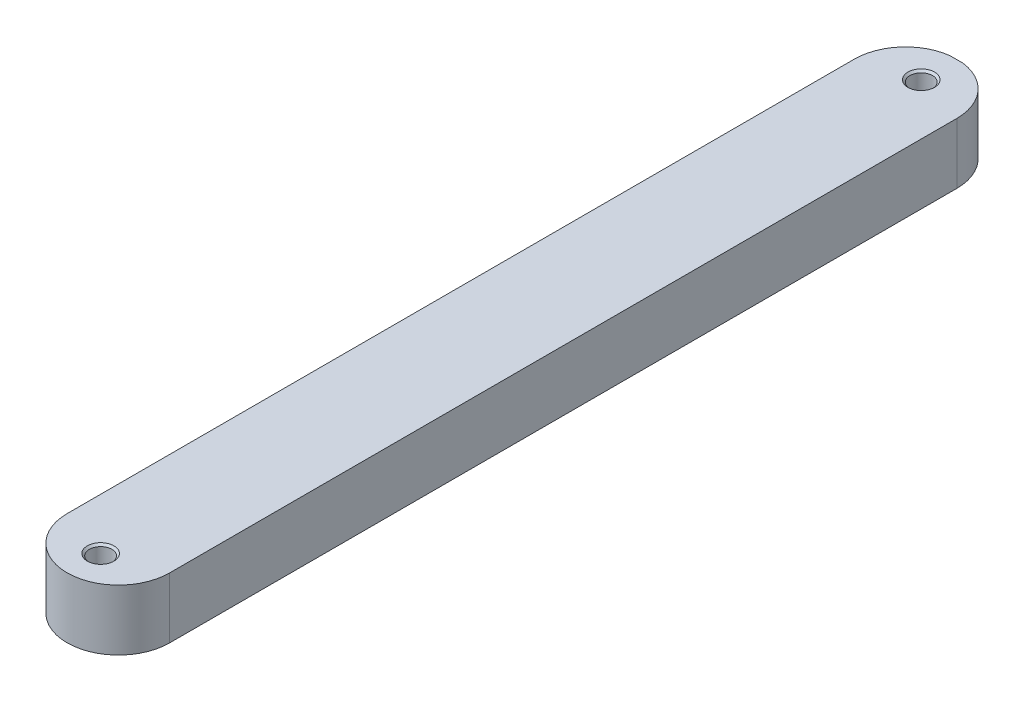
SolidWorks part; units mm, degrees
ref_plane "前视基准面" through (0, 0, 0) normal (0, 0, 1) x (1, 0, 0)
ref_plane "上视基准面" through (0, 0, 0) normal (0, 1, 0) x (1, 0, 0)
ref_plane "右视基准面" through (0, 0, 0) normal (1, 0, 0) x (0, 0, -1)
sketch "草图1" plane through (0, 0, 0) normal (1, 0, 0) x (0, 0, -1)
  line L1 (0, 0) -> (200, 0)
  line L2 (0, 0) -> (0, -20)
  line L3 (0, -20) -> (200, -20)
  line L4 (200, 0) -> (200, -20)
extrude "凸台-拉伸1" add sketch "草图1" along normal blind 30
sketch "草图3" plane through (0, 0, 0) normal (0, 0, 1) x (1, 0, 0)
  line L0 (0, 0) -> (0, -20) construction
  line L1 (0, -1.0813) -> (30, -1.0813)
  line L2 (0, -1.0813) -> (0, -18.8063)
  line L3 (0, -18.8063) -> (30, -18.8063)
  line L4 (30, -1.0813) -> (30, -18.8063)
  line L5 (30, 0) -> (30, -20) construction
extrude "凸台-拉伸2" add sketch "草图3" against normal blind 1 and the other way blind 30
sketch "草图5" plane through (0, -1.0813, 0) normal (0, 1, 0) x (1, 0, 0)
  line L0 (0, -15) -> (30, -15)
  line L1 (30, -15) -> (30, -30)
  line L2 (30, -30) -> (0, -30)
  line L3 (0, -30) -> (0, -15)
  circle A0 centre (15, -15) radius 15
  line M2 (30, -30) -> (30, 0)
  line M4 (0, 0) -> (0, -30)
  line M5 (0, -30) -> (30, -30)
extrude "切除-拉伸1" cut sketch "草图5" against normal blind 18 contours A0 M4 M5 | A0 L2 M2
hole_wizard "G1/16 螺纹孔1" positions "草图6" profile "草图7" tap size "G1/16" standard "GB" end condition up to next
sketch "草图6" plane through (0, -1.0813, 0) normal (0, 1, 0) x (1, 0, 0)
  point P0 (15, -20.2039)
sketch "草图7" plane through (15, -1.0813, 20.2039) normal (1, 0, 0) x (0, 0, 1)
  line L0 (0, 0) -> (0, 17.725)
  line L1 (0, 17.725) -> (3.3, 17.725)
  line L2 (3.3, 17.725) -> (3.3, 0.5865)
  line L3 (3.3, 0.5865) -> (3.8865, 0)
  line L5 (3.8865, 0) -> (0, 0)
  line L6 (-3.3, 0.5865) -> (-3.8865, 0) construction
  line L11 (0, -6.35) -> (0, 107.95) construction
  dimension "通孔螺纹孔钻头直径" = 6.6
  dimension "通孔螺纹孔钻头深度" = 17.725
  dimension "近端锥形沉头孔直径" = 7.773
  dimension "近端锥形沉头孔角度" = 90
cosmetic thread "孔螺蚊线1" parameters "D2"=7.723
sketch "草图9" plane through (0, 0, -200) normal (0, 0, -1) x (-1, 0, 0)
  line L1 (-30, -1.0813) -> (0, -1.0813)
  line L2 (-30, -1.0813) -> (-30, -18.8063)
  line L3 (-30, -18.8063) -> (0, -18.8063)
  line L4 (0, -1.0813) -> (0, -18.8063)
extrude "凸台-拉伸3" add sketch "草图9" along normal blind 30
sketch "草图10" plane through (0, -1.0813, 0) normal (0, 1, 0) x (1, 0, 0)
  line L0 (0, 200) -> (0, 230)
  line L1 (0, 230) -> (30, 230)
  line L2 (30, 230) -> (30, 215.1226)
  circle A0 centre (15, 215.1226) radius 15
  line M2 (30, 200) -> (30, 230)
  line M3 (30, 230) -> (0, 230)
  line M4 (0, 230) -> (0, 200)
extrude "切除-拉伸2" cut sketch "草图10" against normal blind 30 contours A0 M3 M4 | A0 M2 M3
hole_wizard "G1/16 螺纹孔2" positions "草图11" profile "草图12" tap size "G1/16" standard "GB" end condition up to next
sketch "草图11" plane through (0, -1.0813, 0) normal (0, 1, 0) x (1, 0, 0)
  point P0 (15, 219.7016)
sketch "草图12" plane through (15, -1.0813, -219.7016) normal (1, 0, 0) x (0, 0, 1)
  line L0 (0, 0) -> (0, 17.725)
  line L1 (0, 17.725) -> (3.3, 17.725)
  line L2 (3.3, 17.725) -> (3.3, 0.5865)
  line L3 (3.3, 0.5865) -> (3.8865, 0)
  line L5 (3.8865, 0) -> (0, 0)
  line L6 (-3.3, 0.5865) -> (-3.8865, 0) construction
  line L11 (0, -6.35) -> (0, 107.95) construction
  dimension "通孔螺纹孔钻头直径" = 6.6
  dimension "通孔螺纹孔钻头深度" = 17.725
  dimension "近端锥形沉头孔直径" = 7.773
  dimension "近端锥形沉头孔角度" = 90
cosmetic thread "孔螺蚊线2" parameters "D2"=7.723
sketch "草图14" plane through (0, 0, 0) normal (0, 0, 1) x (1, 0, 0)
  line L1 (0, 0) -> (30, 0)
  line L2 (0, 0) -> (0, -1.0813)
  line L3 (0, -1.0813) -> (30, -1.0813)
  line L4 (30, 0) -> (30, -1.0813)
  line L5 (30, -18.8063) -> (0, -18.8063)
  line L6 (30, -18.8063) -> (30, -20)
  line L7 (30, -20) -> (0, -20)
  line L8 (0, -18.8063) -> (0, -20)
extrude "切除-拉伸3" cut sketch "草图14" against normal blind 215
